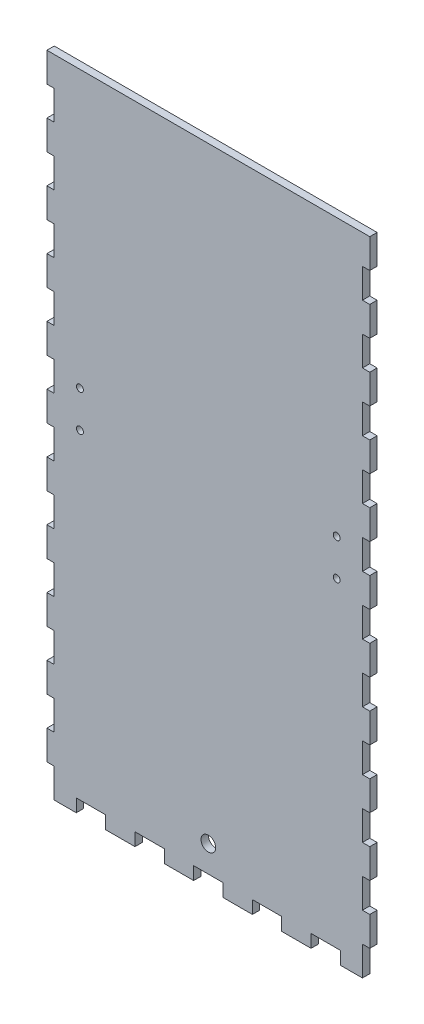
SolidWorks part; units mm, degrees
material "Acrylic (Medium-high impact)"
ref_plane "Front Plane" through (0, 0, 0) normal (0, 0, 1) x (1, 0, 0)
ref_plane "Top Plane" through (0, 0, 0) normal (0, 1, 0) x (1, 0, 0)
ref_plane "Right Plane" through (0, 0, 0) normal (1, 0, 0) x (0, 0, -1)
sketch "Sketch1" plane through (0, 0, 0) normal (0, 0, 1) x (1, 0, 0)
  line L0 (-66.675, 261.112) -> (-66.675, 248.412)
  line L1 (-66.675, 273.812) -> (66.675, 273.812)
  line L2 (-66.675, 273.812) -> (-66.675, 0)
  line L3 (-66.675, 0) -> (66.675, 0)
  line L4 (66.675, 273.812) -> (66.675, 0)
  line L5 (-66.675, 273.812) -> (-69.85, 273.812)
  line L6 (-66.675, 273.812) -> (-66.675, 261.112)
  line L7 (-66.675, 261.112) -> (-69.85, 261.112)
  line L8 (-69.85, 273.812) -> (-69.85, 261.112)
  line L13 (66.675, 273.812) -> (69.85, 273.812)
  line L14 (66.675, 273.812) -> (66.675, 261.112)
  line L15 (66.675, 261.112) -> (69.85, 261.112)
  line L16 (69.85, 273.812) -> (69.85, 261.112)
  line L17 (-66.675, 261.112) -> (-69.85, 261.112)
  line L18 (-69.85, 261.112) -> (-69.85, 248.412)
  line L19 (-66.675, 248.412) -> (-69.85, 248.412)
  line L20 (66.675, 261.112) -> (66.675, 248.412)
  line L21 (66.675, 261.112) -> (69.85, 261.112)
  line L22 (69.85, 261.112) -> (69.85, 248.412)
  line L23 (66.675, 248.412) -> (69.85, 248.412)
  line L24 (-66.675, 248.412) -> (-66.675, 235.712)
  line L25 (-66.675, 248.412) -> (-69.85, 248.412)
  line L26 (-69.85, 248.412) -> (-69.85, 235.712)
  line L27 (-66.675, 235.712) -> (-69.85, 235.712)
  line L28 (66.675, 248.412) -> (66.675, 235.712)
  line L29 (66.675, 248.412) -> (69.85, 248.412)
  line L30 (69.85, 248.412) -> (69.85, 235.712)
  line L31 (66.675, 235.712) -> (69.85, 235.712)
  line L32 (-66.675, 235.712) -> (-66.675, 223.012)
  line L33 (-66.675, 235.712) -> (-69.85, 235.712)
  line L34 (-69.85, 235.712) -> (-69.85, 223.012)
  line L35 (-66.675, 223.012) -> (-69.85, 223.012)
  line L36 (66.675, 235.712) -> (66.675, 223.012)
  line L37 (66.675, 235.712) -> (69.85, 235.712)
  line L38 (69.85, 235.712) -> (69.85, 223.012)
  line L39 (66.675, 223.012) -> (69.85, 223.012)
  line L40 (-66.675, 223.012) -> (-66.675, 210.312)
  line L41 (-66.675, 223.012) -> (-69.85, 223.012)
  line L42 (-69.85, 223.012) -> (-69.85, 210.312)
  line L43 (-66.675, 210.312) -> (-69.85, 210.312)
  line L44 (66.675, 223.012) -> (66.675, 210.312)
  line L45 (66.675, 223.012) -> (69.85, 223.012)
  line L46 (69.85, 223.012) -> (69.85, 210.312)
  line L47 (66.675, 210.312) -> (69.85, 210.312)
  line L48 (-66.675, 210.312) -> (-66.675, 197.612)
  line L49 (-66.675, 210.312) -> (-69.85, 210.312)
  line L50 (-69.85, 210.312) -> (-69.85, 197.612)
  line L51 (-66.675, 197.612) -> (-69.85, 197.612)
  line L52 (66.675, 210.312) -> (66.675, 197.612)
  line L53 (66.675, 210.312) -> (69.85, 210.312)
  line L54 (69.85, 210.312) -> (69.85, 197.612)
  line L55 (66.675, 197.612) -> (69.85, 197.612)
  line L56 (-66.675, 197.612) -> (-66.675, 184.912)
  line L57 (-66.675, 197.612) -> (-69.85, 197.612)
  line L58 (-69.85, 197.612) -> (-69.85, 184.912)
  line L59 (-66.675, 184.912) -> (-69.85, 184.912)
  line L60 (66.675, 197.612) -> (66.675, 184.912)
  line L61 (66.675, 197.612) -> (69.85, 197.612)
  line L62 (69.85, 197.612) -> (69.85, 184.912)
  line L63 (66.675, 184.912) -> (69.85, 184.912)
  line L64 (-66.675, 184.912) -> (-66.675, 172.212)
  line L65 (-66.675, 184.912) -> (-69.85, 184.912)
  line L66 (-69.85, 184.912) -> (-69.85, 172.212)
  line L67 (-66.675, 172.212) -> (-69.85, 172.212)
  line L68 (66.675, 184.912) -> (66.675, 172.212)
  line L69 (66.675, 184.912) -> (69.85, 184.912)
  line L70 (69.85, 184.912) -> (69.85, 172.212)
  line L71 (66.675, 172.212) -> (69.85, 172.212)
  line L72 (-66.675, 172.212) -> (-66.675, 159.512)
  line L73 (-66.675, 172.212) -> (-69.85, 172.212)
  line L74 (-69.85, 172.212) -> (-69.85, 159.512)
  line L75 (-66.675, 159.512) -> (-69.85, 159.512)
  line L76 (66.675, 172.212) -> (66.675, 159.512)
  line L77 (66.675, 172.212) -> (69.85, 172.212)
  line L78 (69.85, 172.212) -> (69.85, 159.512)
  line L79 (66.675, 159.512) -> (69.85, 159.512)
  line L80 (-66.675, 159.512) -> (-66.675, 146.812)
  line L81 (-66.675, 159.512) -> (-69.85, 159.512)
  line L82 (-69.85, 159.512) -> (-69.85, 146.812)
  line L83 (-66.675, 146.812) -> (-69.85, 146.812)
  line L84 (66.675, 159.512) -> (66.675, 146.812)
  line L85 (66.675, 159.512) -> (69.85, 159.512)
  line L86 (69.85, 159.512) -> (69.85, 146.812)
  line L87 (66.675, 146.812) -> (69.85, 146.812)
  line L88 (-66.675, 146.812) -> (-66.675, 134.112)
  line L89 (-66.675, 146.812) -> (-69.85, 146.812)
  line L90 (-69.85, 146.812) -> (-69.85, 134.112)
  line L91 (-66.675, 134.112) -> (-69.85, 134.112)
  line L92 (66.675, 146.812) -> (66.675, 134.112)
  line L93 (66.675, 146.812) -> (69.85, 146.812)
  line L94 (69.85, 146.812) -> (69.85, 134.112)
  line L95 (66.675, 134.112) -> (69.85, 134.112)
  line L96 (-66.675, 134.112) -> (-66.675, 121.412)
  line L97 (-66.675, 134.112) -> (-69.85, 134.112)
  line L98 (-69.85, 134.112) -> (-69.85, 121.412)
  line L99 (-66.675, 121.412) -> (-69.85, 121.412)
  line L100 (66.675, 134.112) -> (66.675, 121.412)
  line L101 (66.675, 134.112) -> (69.85, 134.112)
  line L102 (69.85, 134.112) -> (69.85, 121.412)
  line L103 (66.675, 121.412) -> (69.85, 121.412)
  line L104 (-66.675, 121.412) -> (-66.675, 108.712)
  line L105 (-66.675, 121.412) -> (-69.85, 121.412)
  line L106 (-69.85, 121.412) -> (-69.85, 108.712)
  line L107 (-66.675, 108.712) -> (-69.85, 108.712)
  line L108 (66.675, 121.412) -> (66.675, 108.712)
  line L109 (66.675, 121.412) -> (69.85, 121.412)
  line L110 (69.85, 121.412) -> (69.85, 108.712)
  line L111 (66.675, 108.712) -> (69.85, 108.712)
  line L112 (-66.675, 108.712) -> (-66.675, 96.012)
  line L113 (-66.675, 108.712) -> (-69.85, 108.712)
  line L114 (-69.85, 108.712) -> (-69.85, 96.012)
  line L115 (-66.675, 96.012) -> (-69.85, 96.012)
  line L116 (66.675, 108.712) -> (66.675, 96.012)
  line L117 (66.675, 108.712) -> (69.85, 108.712)
  line L118 (69.85, 108.712) -> (69.85, 96.012)
  line L119 (66.675, 96.012) -> (69.85, 96.012)
  line L120 (-66.675, 96.012) -> (-66.675, 83.312)
  line L121 (-66.675, 96.012) -> (-69.85, 96.012)
  line L122 (-69.85, 96.012) -> (-69.85, 83.312)
  line L123 (-66.675, 83.312) -> (-69.85, 83.312)
  line L124 (66.675, 96.012) -> (66.675, 83.312)
  line L125 (66.675, 96.012) -> (69.85, 96.012)
  line L126 (69.85, 96.012) -> (69.85, 83.312)
  line L127 (66.675, 83.312) -> (69.85, 83.312)
  line L128 (-66.675, 83.312) -> (-66.675, 70.612)
  line L129 (-66.675, 83.312) -> (-69.85, 83.312)
  line L130 (-69.85, 83.312) -> (-69.85, 70.612)
  line L131 (-66.675, 70.612) -> (-69.85, 70.612)
  line L132 (66.675, 83.312) -> (66.675, 70.612)
  line L133 (66.675, 83.312) -> (69.85, 83.312)
  line L134 (69.85, 83.312) -> (69.85, 70.612)
  line L135 (66.675, 70.612) -> (69.85, 70.612)
  line L136 (-66.675, 70.612) -> (-66.675, 57.912)
  line L137 (-66.675, 70.612) -> (-69.85, 70.612)
  line L138 (-69.85, 70.612) -> (-69.85, 57.912)
  line L139 (-66.675, 57.912) -> (-69.85, 57.912)
  line L140 (66.675, 70.612) -> (66.675, 57.912)
  line L141 (66.675, 70.612) -> (69.85, 70.612)
  line L142 (69.85, 70.612) -> (69.85, 57.912)
  line L143 (66.675, 57.912) -> (69.85, 57.912)
  line L144 (-66.675, 57.912) -> (-66.675, 45.212)
  line L145 (-66.675, 57.912) -> (-69.85, 57.912)
  line L146 (-69.85, 57.912) -> (-69.85, 45.212)
  line L147 (-66.675, 45.212) -> (-69.85, 45.212)
  line L148 (66.675, 57.912) -> (66.675, 45.212)
  line L149 (66.675, 57.912) -> (69.85, 57.912)
  line L150 (69.85, 57.912) -> (69.85, 45.212)
  line L151 (66.675, 45.212) -> (69.85, 45.212)
  line L152 (-66.675, 45.212) -> (-66.675, 32.512)
  line L153 (-66.675, 45.212) -> (-69.85, 45.212)
  line L154 (-69.85, 45.212) -> (-69.85, 32.512)
  line L155 (-66.675, 32.512) -> (-69.85, 32.512)
  line L156 (66.675, 45.212) -> (66.675, 32.512)
  line L157 (66.675, 45.212) -> (69.85, 45.212)
  line L158 (69.85, 45.212) -> (69.85, 32.512)
  line L159 (66.675, 32.512) -> (69.85, 32.512)
  line L160 (-66.675, 32.512) -> (-66.675, 19.812)
  line L161 (-66.675, 32.512) -> (-69.85, 32.512)
  line L162 (-69.85, 32.512) -> (-69.85, 19.812)
  line L163 (-66.675, 19.812) -> (-69.85, 19.812)
  line L164 (66.675, 32.512) -> (66.675, 19.812)
  line L165 (66.675, 32.512) -> (69.85, 32.512)
  line L166 (69.85, 32.512) -> (69.85, 19.812)
  line L167 (66.675, 19.812) -> (69.85, 19.812)
  line L168 (-66.675, 19.812) -> (-66.675, 7.112)
  line L169 (-66.675, 19.812) -> (-69.85, 19.812)
  line L170 (-69.85, 19.812) -> (-69.85, 7.112)
  line L171 (-66.675, 7.112) -> (-69.85, 7.112)
  line L172 (66.675, 19.812) -> (66.675, 7.112)
  line L173 (66.675, 19.812) -> (69.85, 19.812)
  line L174 (69.85, 19.812) -> (69.85, 7.112)
  line L175 (66.675, 7.112) -> (69.85, 7.112)
  line L176 (-66.675, 7.112) -> (-66.675, -5.588)
  line L177 (-66.675, 7.112) -> (-69.85, 7.112)
  line L178 (-69.85, 7.112) -> (-69.85, -5.588)
  line L179 (-66.675, -5.588) -> (-69.85, -5.588)
  line L180 (66.675, 7.112) -> (66.675, -5.588)
  line L181 (66.675, 7.112) -> (69.85, 7.112)
  line L182 (69.85, 7.112) -> (69.85, -5.588)
  line L183 (66.675, -5.588) -> (69.85, -5.588)
  line L184 (-57.15, 0) -> (-57.15, -5.588)
  line L185 (-69.85, 0) -> (-57.15, 0)
  line L186 (-69.85, 0) -> (-69.85, -5.588)
  line L187 (-69.85, -5.588) -> (-57.15, -5.588)
  line L188 (-57.15, 0) -> (-57.15, -5.588)
  line L189 (-57.15, 0) -> (-44.45, 0)
  line L190 (-44.45, 0) -> (-44.45, -5.588)
  line L191 (-57.15, -5.588) -> (-44.45, -5.588)
  line L192 (-44.45, 0) -> (-44.45, -5.588)
  line L193 (-44.45, 0) -> (-31.75, 0)
  line L194 (-31.75, 0) -> (-31.75, -5.588)
  line L195 (-44.45, -5.588) -> (-31.75, -5.588)
  line L196 (-31.75, 0) -> (-31.75, -5.588)
  line L197 (-31.75, 0) -> (-19.05, 0)
  line L198 (-19.05, 0) -> (-19.05, -5.588)
  line L199 (-31.75, -5.588) -> (-19.05, -5.588)
  line L200 (-19.05, 0) -> (-19.05, -5.588)
  line L201 (-19.05, 0) -> (-6.35, 0)
  line L202 (-6.35, 0) -> (-6.35, -5.588)
  line L203 (-19.05, -5.588) -> (-6.35, -5.588)
  line L204 (-6.35, 0) -> (-6.35, -5.588)
  line L205 (-6.35, 0) -> (6.35, 0)
  line L206 (6.35, 0) -> (6.35, -5.588)
  line L207 (-6.35, -5.588) -> (6.35, -5.588)
  line L208 (6.35, 0) -> (6.35, -5.588)
  line L209 (6.35, 0) -> (19.05, 0)
  line L210 (19.05, 0) -> (19.05, -5.588)
  line L211 (6.35, -5.588) -> (19.05, -5.588)
  line L212 (19.05, 0) -> (19.05, -5.588)
  line L213 (19.05, 0) -> (31.75, 0)
  line L214 (31.75, 0) -> (31.75, -5.588)
  line L215 (19.05, -5.588) -> (31.75, -5.588)
  line L216 (31.75, 0) -> (31.75, -5.588)
  line L217 (31.75, 0) -> (44.45, 0)
  line L218 (44.45, 0) -> (44.45, -5.588)
  line L219 (31.75, -5.588) -> (44.45, -5.588)
  line L220 (44.45, 0) -> (44.45, -5.588)
  line L221 (44.45, 0) -> (57.15, 0)
  line L222 (57.15, 0) -> (57.15, -5.588)
  line L223 (44.45, -5.588) -> (57.15, -5.588)
  line L224 (57.15, 0) -> (57.15, -5.588)
  line L225 (57.15, 0) -> (69.85, 0)
  line L226 (69.85, 0) -> (69.85, -5.588)
  line L227 (57.15, -5.588) -> (69.85, -5.588)
  point P4 (0, 0)
  dimension "D1" = 133.35
  dimension "D2" = 273.812
  dimension "D3" = 139.7
  dimension "D6" = 279.4
  dimension "D7" = 12.7
  dimension "D8" = 12.7
  dimension "D4" = 22
  dimension "D5" = 11
extrude "Boss-Extrude1" add sketch "Sketch1" along normal blind 3.175 contours L4 L1 L2 L0 L3 | L171 L2 L163 L170 | L155 L2 L147 L154 | L139 L2 L131 L138 | L123 L2 L115 L122 | L176 L187 L184 L3 | L190 L195 L194 L3 | L198 L203 L202 L3 | L206 L211 L210 L3 | L214 L219 L218 L3 | L222 L227 L180 L3 | L4 L175 L174 L167 | L4 L159 L158 L151 | L4 L143 L142 L135 | L4 L127 L126 L119 | L4 L111 L110 L103 | L107 L2 L99 L106 | L91 L2 L83 L90 | L75 L2 L67 L74 | L59 L2 L51 L58 | L43 L2 L35 L42 | L27 L2 L19 L26 | L5 L8 L7 L2 | L4 L95 L94 L87 | L4 L79 L78 L71 | L4 L63 L62 L55 | L4 L47 L46 L39 | L4 L31 L30 L23 | L16 L13 L4 L15
sketch "Sketch2" plane through (0, 0, 3.175) normal (0, 0, 1) x (1, 0, 0)
  circle A0 centre (0, 11.43) radius 3.175
  dimension "D2" = 6.35
  dimension "D1" = 11.43
extrude "Cut-Extrude1" cut sketch "Sketch2" against normal through all
sketch "Sketch3" plane through (0, 0, 3.175) normal (0, 0, 1) x (1, 0, 0)
  line L0 (-55.5625, 154.305) -> (-55.5625, 138.557) construction
  line L1 (55.5625, 154.305) -> (55.5625, 138.557) construction
  line L2 (-55.5625, 146.431) -> (55.5625, 146.431) construction
  line L3 (-57.15, 0) -> (-44.45, 0) construction
  line L5 (-69.85, 146.812) -> (-69.85, 134.112) construction
  circle A0 centre (-55.5625, 154.305) radius 1.5
  circle A1 centre (-55.5625, 138.557) radius 1.5
  circle A2 centre (55.5625, 154.305) radius 1.5
  circle A3 centre (55.5625, 138.557) radius 1.5
  point P10 (0, 146.431)
  dimension "D2" = 3
  dimension "D3" = 138.557
  dimension "D4" = 14.2875
  dimension "D1" = 15.748
extrude "Cut-Extrude2" cut sketch "Sketch3" against normal through all
sketch "Sketch4" plane through (0, 0, 3.175) normal (0, 0, 1) x (1, 0, 0)
  line L0 (-69.85, 273.812) -> (69.85, 273.812) construction
  line L1 (-66.675, 273.812) -> (66.675, 273.812)
  line L2 (-66.675, 273.812) -> (-66.675, 299.212)
  line L3 (-66.675, 299.212) -> (66.675, 299.212)
  line L4 (66.675, 273.812) -> (66.675, 299.212)
  dimension "D1" = 25.4
extrude "Boss-Extrude2" [suppressed] add sketch "Sketch4" against normal up to surface (3.175 mm away)
equation "\"bottomThickness\"= .220in"
equation "\"wallThickness\"= .125in"
equation "\"D3@Sketch1\"=2*\"wallThickness\"+5.25"
equation "\"D6@Sketch1\"=\"bottomThickness\"+10.78"
equation "\"D7@Sketch1\"=\"D6@Sketch1\"/\"D4@Sketch1\""
equation "\"D8@Sketch1\"=\"D3@Sketch1\"/\"D5@Sketch1\""
equation "\"D1@Boss-Extrude1\"=\"wallThickness\""
